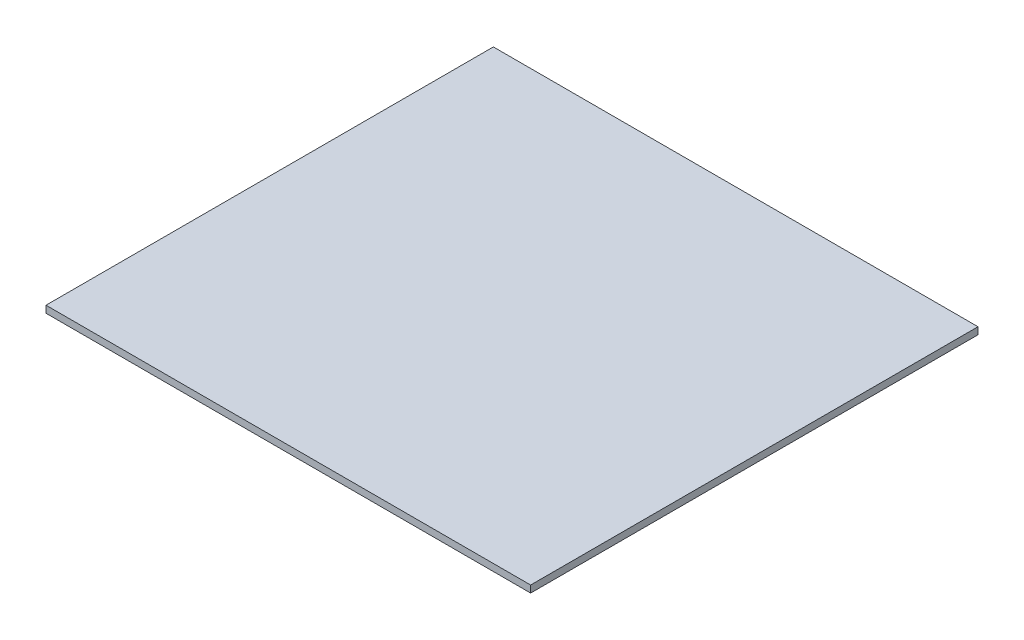
SolidWorks part; units mm, degrees
ref_plane "Front Plane" through (0, 0, 0) normal (0, 0, 1) x (1, 0, 0)
ref_plane "Top Plane" through (0, 0, 0) normal (0, 1, 0) x (1, 0, 0)
ref_plane "Right Plane" through (0, 0, 0) normal (1, 0, 0) x (0, 0, -1)
sketch "Sketch1" plane through (0, 0, 0) normal (0, 1, 0) x (1, 0, 0)
  line L1 (0, 0) -> (330.2, 0)
  line L2 (0, 0) -> (0, -304.8)
  line L3 (0, -304.8) -> (330.2, -304.8)
  line L4 (330.2, 0) -> (330.2, -304.8)
  dimension "D1" = 304.8
  dimension "D2" = 330.2
extrude "Boss-Extrude1" add sketch "Sketch1" along normal blind 4.7625 contours L1 L4 L3 L2
